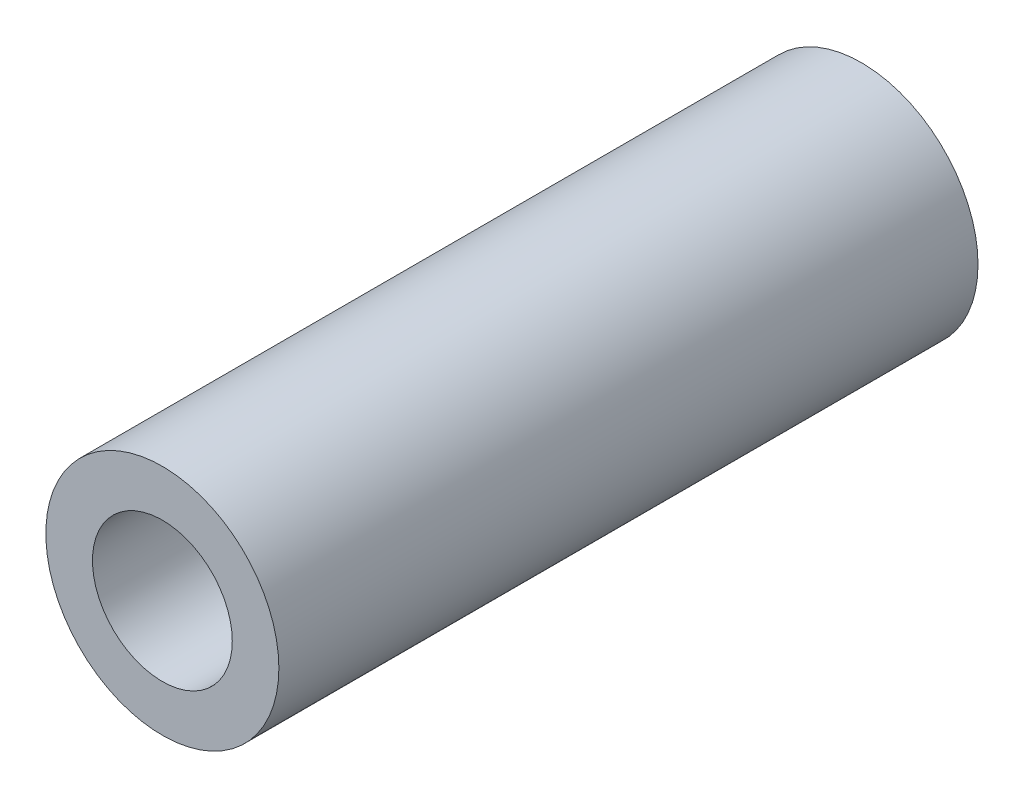
SolidWorks part; units mm, degrees
ref_plane "前视基准面" through (0, 0, 0) normal (0, 0, 1) x (1, 0, 0)
ref_plane "上视基准面" through (0, 0, 0) normal (0, 1, 0) x (1, 0, 0)
ref_plane "右视基准面" through (0, 0, 0) normal (1, 0, 0) x (0, 0, -1)
sketch "草图1" plane through (0, 0, 0) normal (0, 0, 1) x (1, 0, 0)
  circle A0 centre (0, 0) radius 2.5
  circle A1 centre (0, 0) radius 1.5
  dimension "D1" = 3
  dimension "D2" = 5
extrude "凸台-拉伸1" add sketch "草图1" along normal mid plane 15
